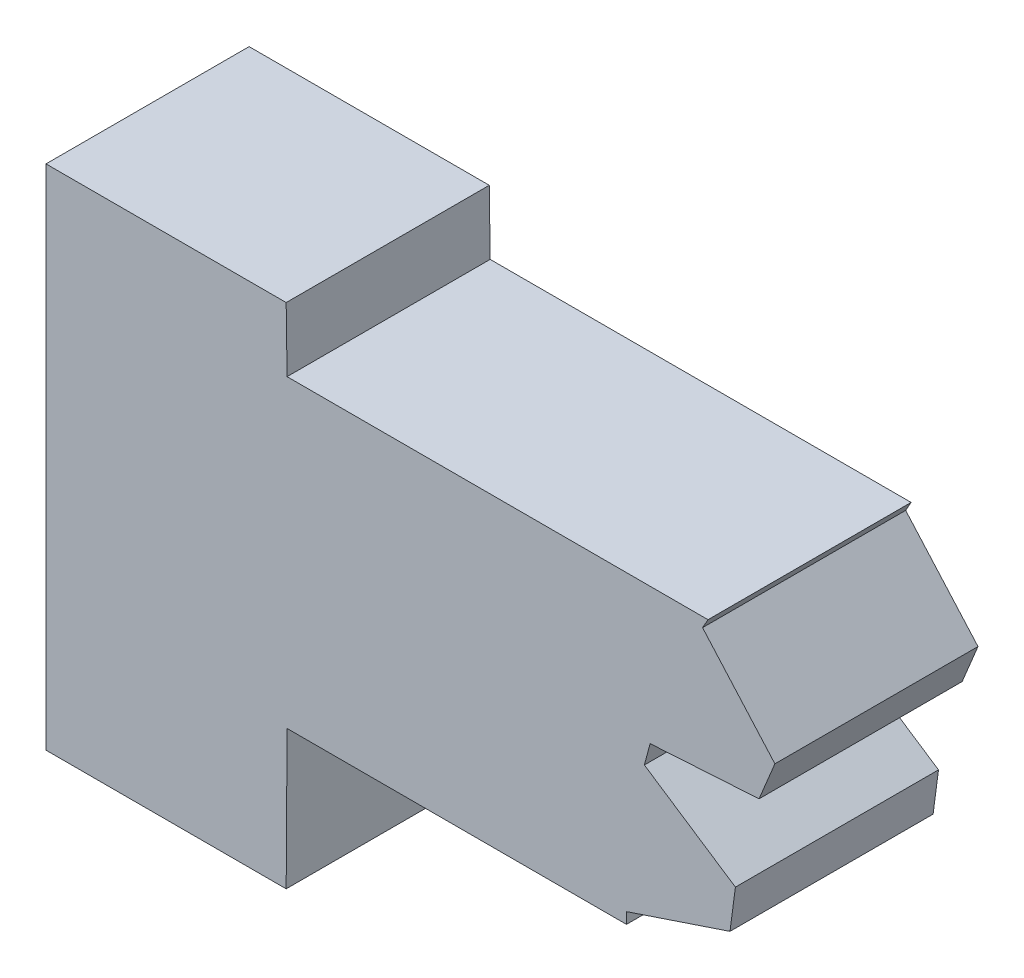
SolidWorks part; units mm, degrees
ref_plane "Front Plane" through (0, 0, 0) normal (0, 0, 1) x (1, 0, 0)
ref_plane "Top Plane" through (0, 0, 0) normal (0, 1, 0) x (1, 0, 0)
ref_plane "Right Plane" through (0, 0, 0) normal (1, 0, 0) x (0, 0, -1)
sketch "Sketch1" plane through (0, 0, 0) normal (0, 0, 1) x (1, 0, 0)
  line L0 (4.7478, 2.7448) -> (11.4321, 2.7448)
  line L1 (4.7478, 2.7448) -> (4.73, 0)
  line L2 (4.7478, 8.7448) -> (13.0378, 8.7448)
  line L3 (11.4321, 2.7448) -> (11.4321, 2.9629)
  line L4 (4.73, 0) -> (0, 0)
  line L5 (11.4321, 2.9629) -> (13.4707, 3.6448)
  line L6 (13.4707, 3.6448) -> (13.5771, 4.4531)
  line L7 (13.5771, 4.4531) -> (11.7845, 5.6394)
  line L8 (11.7845, 5.6394) -> (11.8973, 6.0607)
  line L9 (11.8973, 6.0607) -> (14.043, 6.1918)
  line L10 (14.043, 6.1918) -> (14.355, 6.9451)
  line L11 (14.355, 6.9451) -> (12.9305, 8.5549)
  line L12 (12.9305, 8.5549) -> (13.0378, 8.7448)
  line L13 (4.73, 10) -> (0, 10)
  line L14 (0, 0) -> (0, 10)
  line L15 (4.73, 10) -> (4.7478, 8.7448)
  dimension "D1" = 4.73
  dimension "D2" = 4.7478
  dimension "D3" = 1.2552
  dimension "D4" = 8.29
  dimension "D5" = 0.4362
  dimension "D6" = 2.1496
  dimension "D7" = 0.8153
  dimension "D8" = 0.2181
  dimension "D9" = 8.5549
  dimension "D10" = 6.9451
  dimension "D11" = 6.1918
  dimension "D12" = 6.0607
  dimension "D13" = 2.7448
  dimension "D14" = 5.6394
  dimension "D15" = 4.4531
  dimension "D16" = 3.6448
  dimension "D23" = 10
extrude "Boss-Extrude1" add sketch "Sketch1" along normal blind 4
equation "\"D4@Sketch1\"= \"ThumbLinkLengthMCP@Sketch1@thumbMovingBracketDown.SLDPRT\" - 10.7 'Toothed Mechanism"
